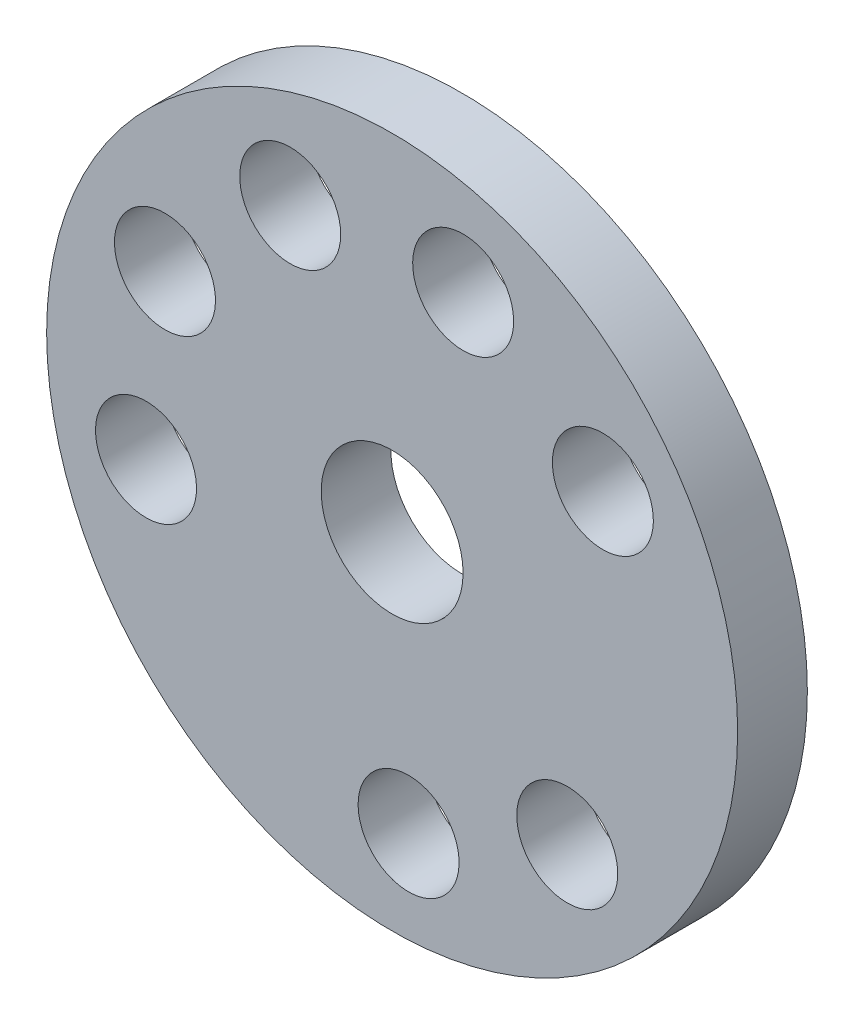
SolidWorks part; units mm, degrees
material "Brass"
ref_plane "Front Plane" through (0, 0, 0) normal (0, 0, 1) x (1, 0, 0)
ref_plane "Top Plane" through (0, 0, 0) normal (0, 1, 0) x (1, 0, 0)
ref_plane "Right Plane" through (0, 0, 0) normal (1, 0, 0) x (0, 0, -1)
sketch "Sketch8" plane through (0, 0, 0) normal (0, 0, 1) x (1, 0, 0)
  circle A0 centre (0, 0) radius 49.5648
extrude "Boss-Extrude3" add sketch "Sketch8" along normal blind 10
sketch "Sketch9" plane through (0, 0, 10) normal (0, 0, 1) x (1, 0, 0)
  circle A0 centre (0, 0) radius 10.1766
extrude "Cut-Extrude3" cut sketch "Sketch9" against normal through all
sketch "Sketch11" plane through (0, 0, 10) normal (0, 0, 1) x (1, 0, 0)
  circle A0 centre (-14.6214, 33.2739) radius 7.2424
extrude "Cut-Extrude5" cut sketch "Sketch11" against normal through all
pattern_circular "CirPattern2" count 9 every 40 about axis through (0, 0, 0) along (0, 0, 1) skipping 3, 6 of "Cut-Extrude5"
